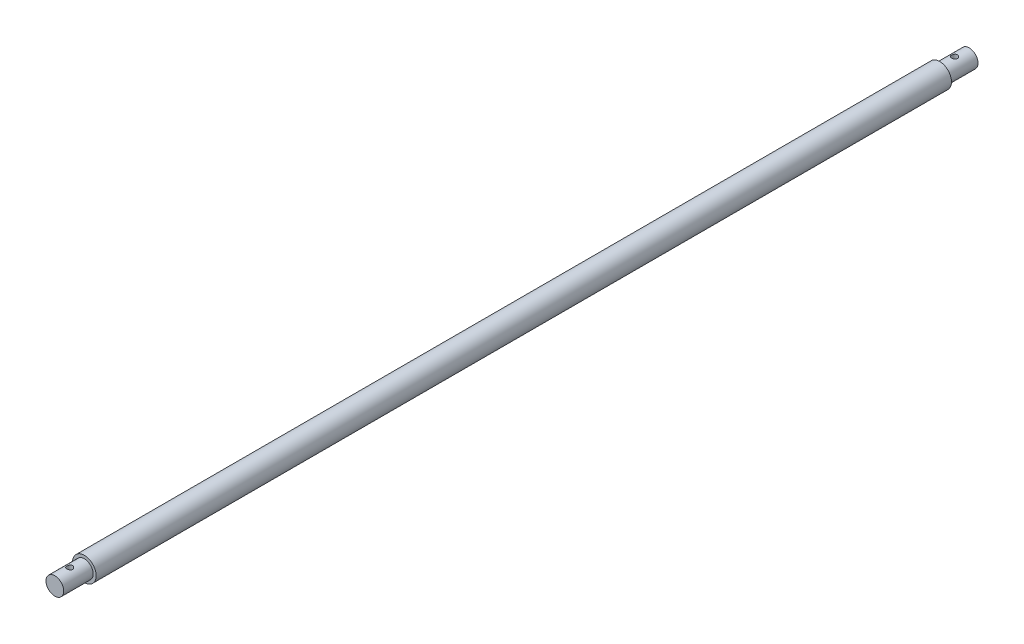
SolidWorks part; units mm, degrees
material "Plain Carbon Steel"
ref_plane "Front Plane" through (0, 0, 0) normal (0, 0, 1) x (1, 0, 0)
ref_plane "Top Plane" through (0, 0, 0) normal (0, 1, 0) x (1, 0, 0)
ref_plane "Right Plane" through (0, 0, 0) normal (1, 0, 0) x (0, 0, -1)
sketch "Sketch1" plane through (0, 0, 0) normal (0, 0, 1) x (1, 0, 0)
  circle A0 centre (0, 0) radius 4
  dimension "D1" = 8
extrude "Boss-Extrude1" add sketch "Sketch1" along normal blind 300
sketch "Sketch2" plane through (0, 0, 300) normal (0, 0, 1) x (1, 0, 0)
  circle A0 centre (0, 0) radius 3
extrude "Boss-Extrude2" add sketch "Sketch2" along normal blind 10
sketch "Sketch3" plane through (0, 0, 0) normal (0, 1, 0) x (1, 0, 0)
  line L0 (-3, -310) -> (3, -310) construction
  line L1 (-3, -300) -> (-3, -310) construction
  circle A0 centre (0, -305) radius 1
  dimension "D1" = 2
  dimension "D2" = 5
  dimension "D3" = 3
extrude "Cut-Extrude1" cut sketch "Sketch3" along normal mid plane 6
sketch "Sketch4" plane through (0, 0, 0) normal (0, 0, -1) x (-1, 0, 0)
  circle A0 centre (0, 0) radius 4
  circle A1 centre (0, 0) radius 3
  dimension "D1" = 8
  dimension "D2" = 6
extrude "Cut-Extrude2" cut sketch "Sketch4" against normal blind 10
sketch "Sketch5" plane through (0, 0, 0) normal (0, 1, 0) x (1, 0, 0)
  line L0 (3, -10) -> (3, 0) construction
  line L1 (3, 0) -> (-3, 0) construction
  circle A0 centre (0, -5) radius 1
  dimension "D1" = 2
  dimension "D2" = 3
  dimension "D3" = 5
extrude "Cut-Extrude3" cut sketch "Sketch5" along normal mid plane 6
